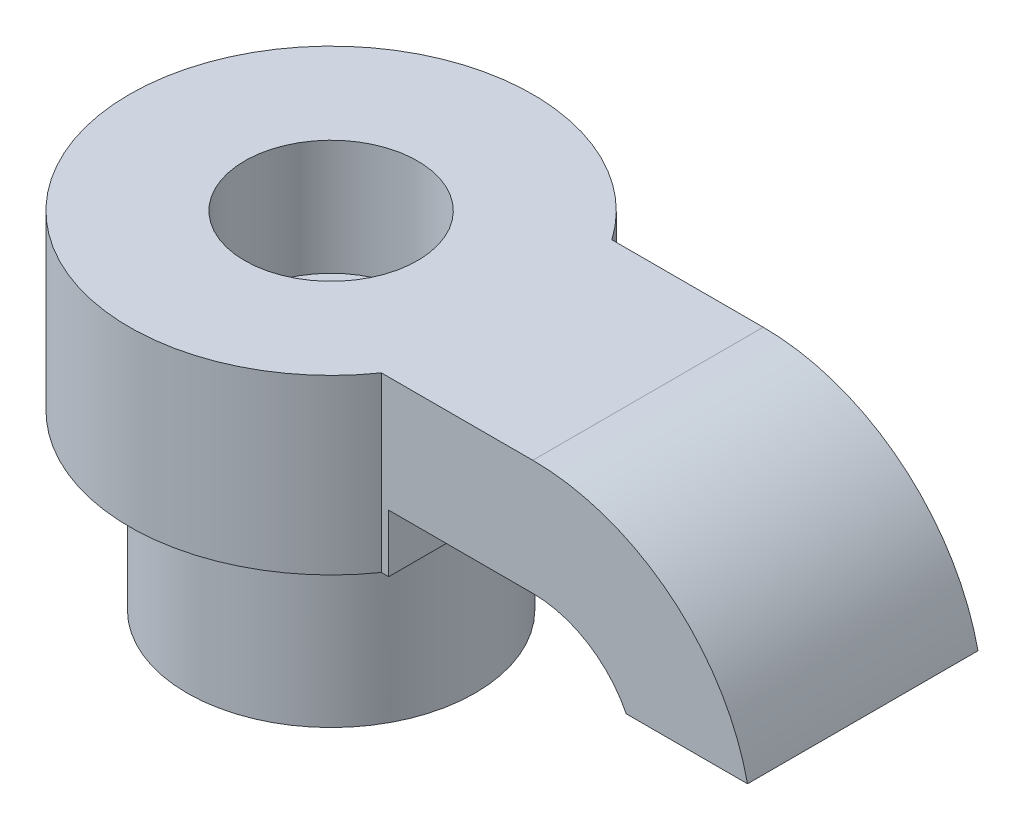
SolidWorks part; units mm, degrees
ref_plane "前视基准面" through (0, 0, 0) normal (0, 0, 1) x (1, 0, 0)
ref_plane "上视基准面" through (0, 0, 0) normal (0, 1, 0) x (1, 0, 0)
ref_plane "右视基准面" through (0, 0, 0) normal (1, 0, 0) x (0, 0, -1)
sketch "草图3" plane through (0, 0, 0) normal (0, 0, 1) x (1, 0, 0)
  line L0 (0, 0) -> (5, 0)
  line L1 (0, 0) -> (0, -4)
  line L2 (0, -4) -> (5, -4)
  line L3 (8.2435, -6) -> (12.454, -6)
  arc A0 (5, 0) -> (12.454, -6) centre (5, -7.6301) cw
  arc A1 (5, -4) -> (8.2435, -6) centre (5, -7.6301) cw
  dimension "D1" = 6
  dimension "D2" = 4
  dimension "D3" = 5
extrude "凸台-拉伸1" add sketch "草图3" along normal blind 8
sketch "草图4" plane through (0, 0, 0) normal (0, 1, 0) x (1, 0, 0)
  line L0 (0, -8) -> (0, 0) construction
  line L1 (-0.2554, 0) -> (0, 0)
  line L2 (5, 0) -> (0, 0) construction
  line L3 (0, 0) -> (0, -8)
  line L4 (0, -8) -> (-0.2554, -8)
  line L5 (5, -8) -> (0, -8) construction
  arc A0 (-0.2554, 0) -> (-0.2554, -8) centre (-6, -4) ccw
  dimension "D1" = 14
  dimension "D2" = 6
extrude "凸台-拉伸2" add sketch "草图4" against normal blind 6
sketch "草图5" plane through (0, -6, 0) normal (0, -1, 0) x (1, 0, 0)
  circle A0 centre (-6, 4) radius 5
  dimension "D1" = 10
extrude "凸台-拉伸3" add sketch "草图5" along normal blind 6
hole_wizard "孔1" positions "3D草图2" profile "草图6" legacy
sketch3d "3D草图2"
  arc A0 (-0.2554, 0, 0) -> (-0.2554, 0, 8) centre (-6, 0, 4) ccw construction
  point P0 (-6, 0, 4)
  point P6 (-6, 7, 4)
  dimension "D1" = 0
sketch "草图6" plane through (-6, 0, 4) normal (1, 0, 0) x (0, 0, 1)
  line L0 (0, 0) -> (0, 30)
  line L1 (0, 30) -> (1.5, 30)
  line L2 (1.5, 30) -> (1.5, 4)
  line L3 (1.5, 4) -> (3, 4)
  line L4 (3, 4) -> (3, 0)
  line L5 (3, 0) -> (0, 0)
  line L6 (0, 110) -> (0, -10) construction
  dimension "直径" = 3
  dimension "深度" = 30
  dimension "柱坑直径" = 6
  dimension "柱坑深度" = 4
cosmetic thread "装饰螺纹线1" parameters "D2"=15
